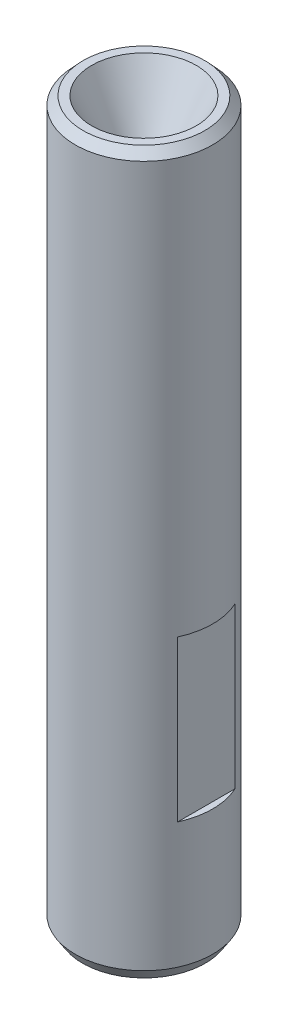
SolidWorks part; units mm, degrees
ref_plane "前视基准面" through (0, 0, 0) normal (0, 0, 1) x (1, 0, 0)
ref_plane "上视基准面" through (0, 0, 0) normal (0, 1, 0) x (1, 0, 0)
ref_plane "右视基准面" through (0, 0, 0) normal (1, 0, 0) x (0, 0, -1)
sketch "草图1" plane through (0, 0, 0) normal (0, 0, 1) x (1, 0, 0)
  line L0 (0, 27) -> (0, 0) construction
  line L1 (-35.3613, 0) -> (38.7816, 0) construction
  line L2 (0, 0) -> (1.1311, 0)
  line L3 (1.45, 0.5) -> (1.45, 31.1313)
  line L4 (0, 0) -> (0, 27)
  line L5 (0, 27) -> (-0.525, 27)
  line L6 (1.1062, 31.5) -> (0.7375, 31.5)
  line L7 (-0.525, 27) -> (-0.525, 29)
  line L8 (-0.525, 29) -> (0.7375, 31.5)
  line L9 (-1.55, 0) -> (-1.55, -3.0407) construction
  line L10 (1.1311, 0) -> (1.45, 0.5)
  line L11 (1.1062, 31.5) -> (1.45, 31.1313)
  line L12 (-1.55, 0) -> (-1.55, 29.8582) construction
  dimension "D2" = 3
  dimension "D3" = 0.5
  dimension "D4" = 1.55
  dimension "D5" = 1.025
  dimension "D6" = 2
  dimension "D7" = 31.5
  dimension "D8" = 2.2875
  dimension "D9" = 2.6562
  dimension "D10" = 0.3687
  dimension "D11" = 2.5
  dimension "D12" = 1.1311
revolve "旋转1" add sketch "草图1" angle 360 about L9
cosmetic thread "装饰螺纹线2"
sketch "草图2" plane through (0, 0, 0) normal (0, 0, 1) x (1, 0, 0)
  line L0 (-1.525, 28.1316) -> (-1.525, 20.4565) construction
  line L1 (-4.6317, 13) -> (-4.6317, 6)
  line L2 (-4.225, 13) -> (-4.225, 6)
  line L3 (-4.6317, 6) -> (-4.225, 6)
  line L4 (1.5817, 6) -> (1.175, 6)
  line L5 (-4.225, 13) -> (-4.6317, 13)
  line L6 (1.175, 13) -> (1.175, 6)
  line L7 (1.5817, 13) -> (1.5817, 6)
  line L8 (1.175, 13) -> (1.5817, 13)
  line L12 (-4.2311, 0) -> (1.1311, 0) construction
  dimension "D1" = 2.7
  dimension "D2" = 7
  dimension "D3" = 6
extrude "切除-拉伸1" cut sketch "草图2" against normal mid plane 10
